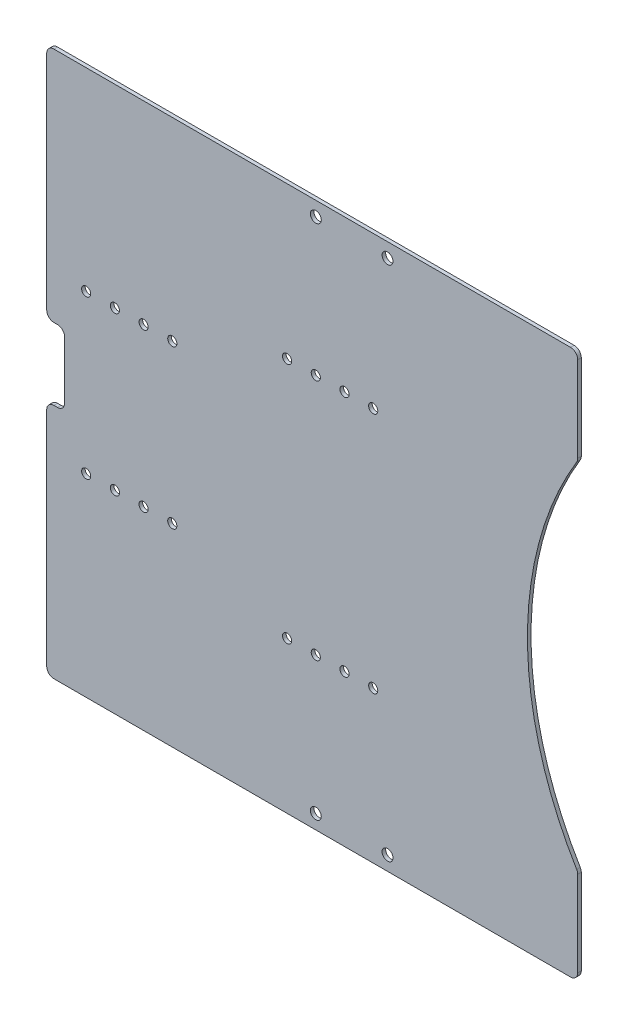
SolidWorks part; units mm, degrees
material "Thornel Mat VMA"
ref_plane "前视基准面" through (0, 0, 0) normal (0, 0, 1) x (1, 0, 0)
ref_plane "上视基准面" through (0, 0, 0) normal (0, 1, 0) x (1, 0, 0)
ref_plane "右视基准面" through (0, 0, 0) normal (1, 0, 0) x (0, 0, -1)
other "Configuration Table"
sketch "草图1" plane through (0, 0, 0) normal (0, 0, 1) x (1, 0, 0)
  line L0 (0, 0) -> (50000, 0) construction
  line L1 (-10, -72) -> (10, -72) construction
  line L2 (-10, -72) -> (-10, 72) construction
  line L3 (-10, 72) -> (10, 72) construction
  line L4 (10, -72) -> (10, 72) construction
  line L5 (-10, -72) -> (10, 72) construction
  line L6 (-10, 72) -> (10, -72) construction
  line L8 (34, -76) -> (-55, -76)
  line L9 (34, -76) -> (34, 76)
  line L10 (34, 76) -> (-55, 76)
  line L11 (-55, -76) -> (-55, 76)
  line L12 (34, -76) -> (-55, 76) construction
  line L13 (34, 76) -> (-55, -76) construction
  circle A0 centre (-10, 72) radius 1.525
  circle A1 centre (10, 72) radius 1.525
  circle A2 centre (10, -72) radius 1.525
  circle A3 centre (-10, -72) radius 1.525
  point P0 (0, 0)
  point P12 (-10.5, 0)
  dimension "D1" = 3.05
  dimension "D2" = 20
  dimension "D3" = 144
  dimension "D4" = 45
  dimension "D5" = 4
  dimension "D6" = 24
extrude "凸台-拉伸1" add sketch "草图1" along normal mid plane 1
sketch "草图2" plane through (0, 0, 0.5) normal (0, 0, 1) x (1, 0, 0)
  line L0 (0, 0) -> (50000, 0) construction
  line L1 (-50, 22) -> (-50, -22) construction
  line L2 (6, 33.75) -> (6, -33.75) construction
  line L3 (-55, 76) -> (-55, -76) construction
  circle A0 centre (-50, 22) radius 1.275
  circle A1 centre (-50, -22) radius 1.275
  circle A2 centre (6, -33.75) radius 1.275
  circle A3 centre (6, 33.75) radius 1.275
  point P6 (-50, 0)
  point P9 (6, 0)
  dimension "D4" = 2.55
  dimension "D1" = 44
  dimension "D2" = 56
  dimension "D3" = 67.5
  dimension "D5" = 5
extrude "切除-拉伸1" cut sketch "草图2" against normal mid plane 10
sketch "草图4" plane through (0, 0, 0.5) normal (0, 0, 1) x (1, 0, 0)
  line L1 (34, 76) -> (63, 76)
  line L2 (34, 76) -> (34, -76)
  line L3 (34, -76) -> (63, -76)
  line L4 (63, 76) -> (63, -76)
  dimension "D1" = 29
extrude "凸台-拉伸3" add sketch "草图4" against normal up to surface (1 mm away) up to face at (7.275, 33.75, -0.5)
sketch "草图5" plane through (0, 0, 0.5) normal (0, 0, 1) x (1, 0, 0)
  circle A0 centre (144, 0) radius 95
  dimension "D1" = 190
extrude "切除-拉伸3" cut sketch "草图5" against normal blind 22
sketch "草图9" plane through (0, 0, 0.5) normal (0, 0, 1) x (1, 0, 0)
  line L1 (-55, 76) -> (-85, 76)
  line L2 (-55, 76) -> (-55, -76)
  line L3 (-55, -76) -> (-85, -76)
  line L4 (-85, 76) -> (-85, -76)
  dimension "D1" = 30
extrude "凸台-拉伸4" add sketch "草图9" against normal up to surface (1 mm away)
pattern_linear "阵列(线性)1" count 4 spacing 8 along (-1, 0, 0) of "切除-拉伸1"
sketch "草图10" plane through (0, 0, 0.5) normal (0, 0, 1) x (1, 0, 0)
  line L0 (0, 0) -> (50000, 0) construction
  line L1 (-85, 76) -> (-85, -76) construction
  line L2 (-90, 10) -> (-80, 10)
  line L3 (-90, 10) -> (-90, -10)
  line L4 (-90, -10) -> (-80, -10)
  line L5 (-80, 10) -> (-80, -10)
  line L6 (-90, 10) -> (-80, -10) construction
  line L7 (-90, -10) -> (-80, 10) construction
  point P3 (-85, 0)
  dimension "D1" = 10
  dimension "D2" = 20
extrude "切除-拉伸4" cut sketch "草图10" against normal blind 10
fillet "圆角1" radius 2 10 edges at (-85, -76, 0) (63, -76, 0) (63, 49.6387, 0) (63, -49.6387, 0) (63, 76, 0) (-85, 76, 0) (-85, 10, 0) (-80, -10, 0) (-85, -10, 0) (-80, 10, 0)
